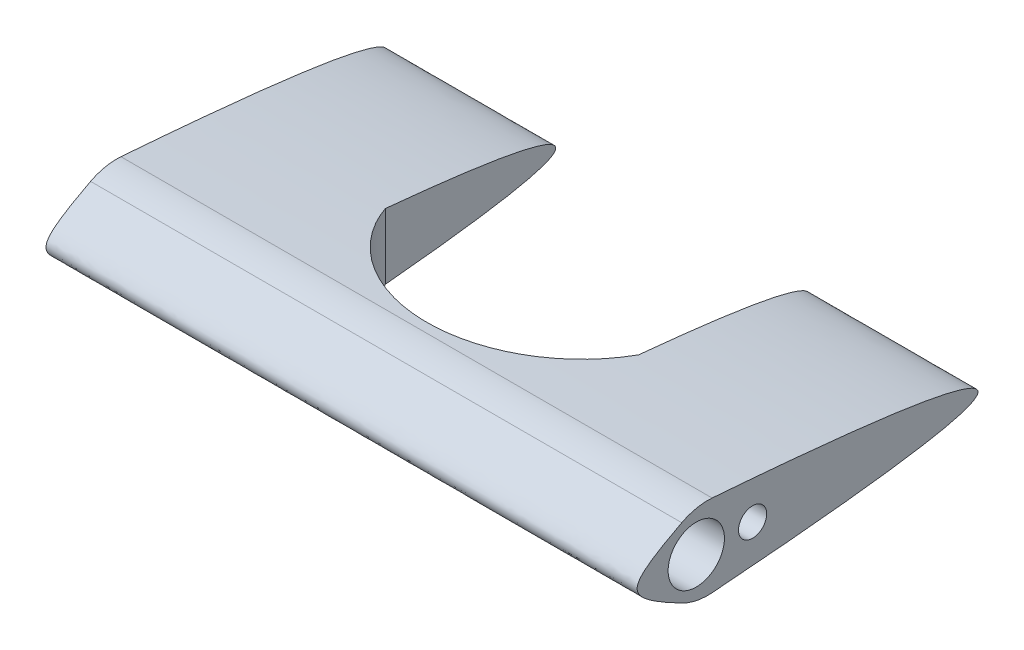
SolidWorks part; units mm, degrees
ref_plane "Front Plane" through (0, 0, 0) normal (0, 0, 1) x (1, 0, 0)
ref_plane "Top Plane" through (0, 0, 0) normal (0, 1, 0) x (1, 0, 0)
ref_plane "Right Plane" through (0, 0, 0) normal (1, 0, 0) x (0, 0, -1)
sketch "Sketch1" plane through (0, 0, 0) normal (1, 0, 0) x (0, 0, -1)
  line L0 (0, -7.6228) -> (0, 2.3772) construction
  line L1 (0, -7.5) -> (0, 7.5) construction
  line L2 (0, 0) -> (-15, 0) construction
  line L3 (0, 0) -> (50, 0) construction
  line L4 (50, 0) -> (75, 0) construction
  line L5 (75, 0) -> (100, 0) construction
  circle A0 centre (0, 0) radius 5
  circle A1 centre (10, 0) radius 2.5
  conic Q0 (0, 7.5) -> (0, -7.5) control (-15, 0) rho 0.7
  conic Q1 (0, 7.5) -> (0, -7.5) control (100, 0) rho 0.500367
  point P8 (0, 0)
  dimension "D1" = 10
  dimension "D7" = 5
  dimension "D2" = 15
  dimension "D3" = 15
  dimension "D4" = 50
  dimension "D5" = 25
  dimension "D6" = 25
  dimension "D8" = 10
extrude "Boss-Extrude1" add sketch "Sketch1" along normal blind 105
fillet "Fillet1" radius 10 2 edges at (52.5, 7.5, 0) (52.5, -7.5, 0)
sketch "Sketch2" plane through (0, 0, 0) normal (0, 1, 0) x (1, 0, 0)
  line L0 (0, 2.8086) -> (0, -2.5828) construction
  line L1 (0, -2.5828) -> (0, -10.5) construction
  line L2 (0, -10.5) -> (105, -10.5) construction
  line L3 (105, -10.5) -> (105, -2.5828) construction
  line L4 (105, -2.5828) -> (105, 2.8086) construction
  line L5 (105, 2.8086) -> (105, 50.0367) construction
  line L6 (105, 50.0367) -> (0, 50.0367) construction
  line L7 (0, 50.0367) -> (0, 2.8086) construction
  line L8 (0, 2.8086) -> (0, -2.5828)
  line L9 (0, -2.5828) -> (0, -10.5)
  line L10 (0, -10.5) -> (105, -10.5)
  line L11 (105, -10.5) -> (105, -2.5828)
  line L12 (105, -2.5828) -> (105, 2.8086)
  line L13 (105, 2.8086) -> (105, 50.0367)
  line L14 (105, 50.0367) -> (0, 50.0367)
  line L15 (0, 50.0367) -> (0, 2.8086)
  line L16 (30, 19.7683) -> (75, 19.7683) construction
  line L17 (30, -10.5) -> (75, -10.5)
  line L18 (30, -10.5) -> (30, 50.0367)
  line L19 (30, 50.0367) -> (75, 50.0367)
  line L20 (75, -10.5) -> (75, 50.0367)
  line L21 (30, -10.5) -> (75, 50.0367) construction
  line L22 (30, 50.0367) -> (75, -10.5) construction
  line L23 (52.5, 19.7683) -> (52.5, 50.0367) construction
  line L24 (52.5, -10.5) -> (52.5, 19.7683) construction
  line L25 (75, 34.9025) -> (30, 34.9025) construction
  line L26 (75, 4.6342) -> (30, 4.6342) construction
  arc A0 (30, 19.7683) -> (75, 19.7683) centre (52.5, 10.61) cw
  arc A1 (30, 19.7683) -> (75, 19.7683) centre (52.5, 28.9267) ccw
  point P12 (52.5, 19.7683)
  point P21 (52.5, 34.9025)
  point P24 (52.5, 4.6342)
  dimension "D1" = 30
  dimension "D2" = 30
extrude "Cut-Extrude1" cut sketch "Sketch2" against normal through all both and the other way through all contours L18 A1 L20 A0 | L18 A0 L20 L14
